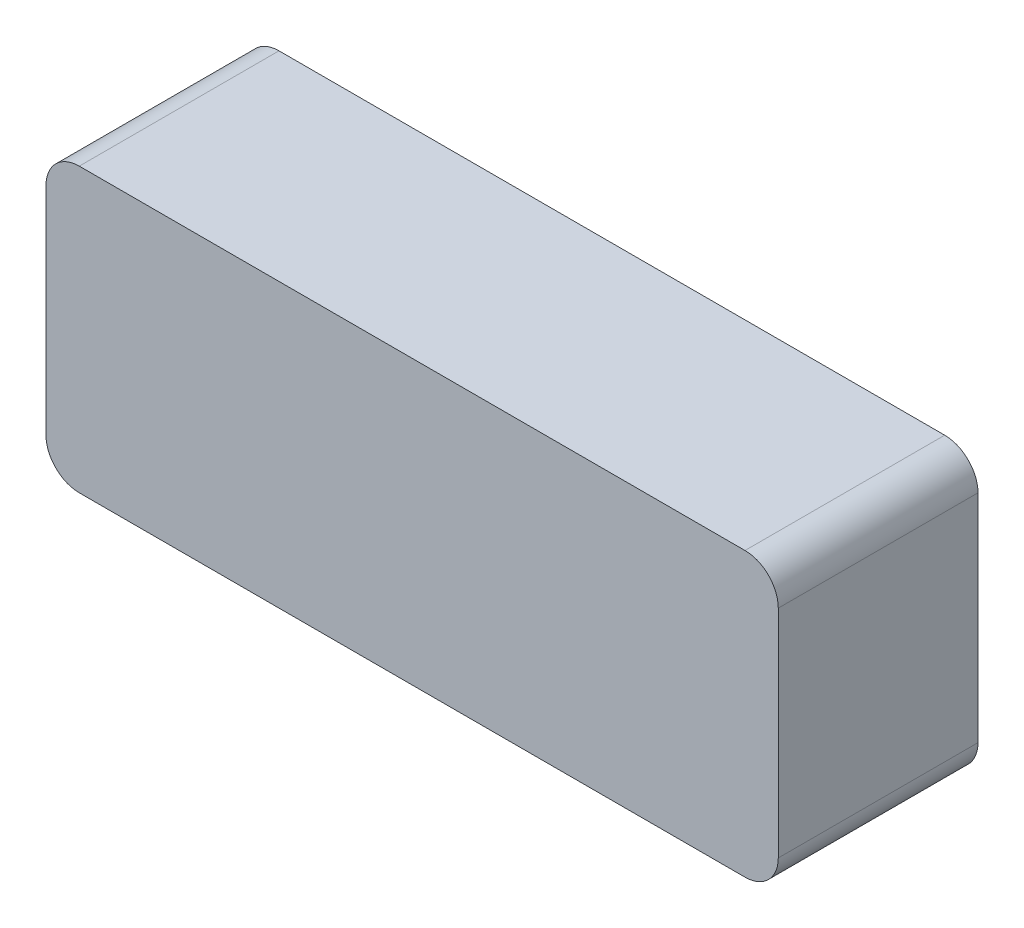
SolidWorks part; units mm, degrees
ref_plane "Plano frontal" through (0, 0, 0) normal (0, 0, 1) x (1, 0, 0)
ref_plane "Plano superior" through (0, 0, 0) normal (0, 1, 0) x (1, 0, 0)
ref_plane "Plano direito" through (0, 0, 0) normal (1, 0, 0) x (0, 0, -1)
sketch "Esboço1" plane through (0, 0, 0) normal (0, 0, 1) x (1, 0, 0)
  line L1 (0, 0) -> (44, 0)
  line L2 (0, 0) -> (0, -17)
  line L3 (0, -17) -> (44, -17)
  line L4 (44, 0) -> (44, -17)
  dimension "D1" = 17
  dimension "36" = 44
extrude "Ressalto-extrusão1" add sketch "Esboço1" along normal blind 12
fillet "Filete1" radius 2 4 edges at (44, -17, 6) (0, -17, 6) (0, 0, 6) (44, 0, 6)
